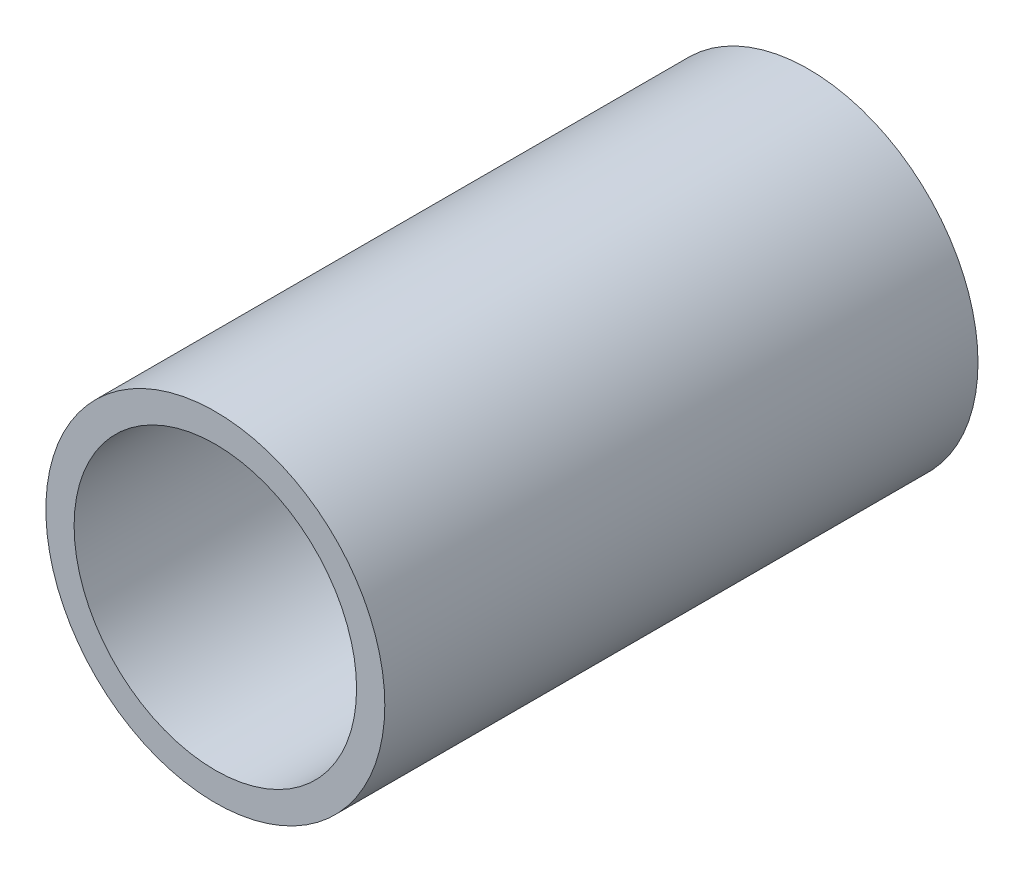
SolidWorks part; units mm, degrees
ref_plane "Front Plane" through (0, 0, 0) normal (0, 0, 1) x (1, 0, 0)
ref_plane "Top Plane" through (0, 0, 0) normal (0, 1, 0) x (1, 0, 0)
ref_plane "Right Plane" through (0, 0, 0) normal (1, 0, 0) x (0, 0, -1)
sketch "Sketch1" plane through (0, 0, 0) normal (0, 0, 1) x (1, 0, 0)
  circle A0 centre (0, 0) radius 11
  dimension "D1" = 22
extrude "Extrude-Thin1" add sketch "Sketch1" along normal mid plane 42 thin thin type mid plane wall 2
